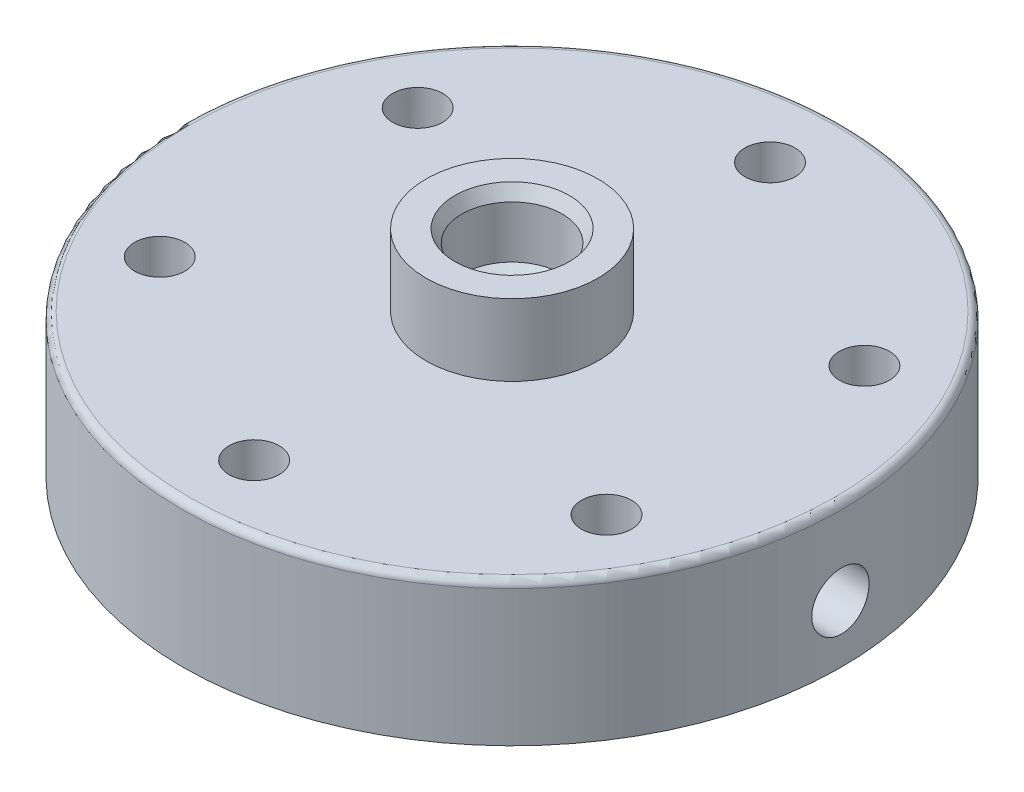
SolidWorks part; units mm, degrees
ref_plane "Front Plane" through (0, 0, 0) normal (0, 0, 1) x (1, 0, 0)
ref_plane "Top Plane" through (0, 0, 0) normal (0, 1, 0) x (1, 0, 0)
ref_plane "Right Plane" through (0, 0, 0) normal (1, 0, 0) x (0, 0, -1)
sketch "Sketch3" plane through (0, 0, 0) normal (0, 1, 0) x (1, 0, 0)
  circle A0 centre (0, 0) radius 46
  circle A1 centre (0, 0) radius 36 construction
  circle A2 centre (0, 36) radius 3.5
  circle A3 centre (31.1769, 18) radius 3.5
  circle A4 centre (31.1769, -18) radius 3.5
  circle A5 centre (0, -36) radius 3.5
  circle A6 centre (-31.1769, -18) radius 3.5
  circle A7 centre (-31.1769, 18) radius 3.5
  dimension "D1" = 92
  dimension "D2" = 72
  dimension "D3" = 7
  dimension "D4" = 6
extrude "Boss-Extrude2" add sketch "Sketch3" along normal blind 20
fillet "Fillet1" radius 1 1 edges at (0, 20, 46)
sketch "Sketch4" plane through (0, 20, 0) normal (0, 1, 0) x (1, 0, 0)
  circle A0 centre (0, 0) radius 12
  dimension "D1" = 24
extrude "Boss-Extrude3" add sketch "Sketch4" along normal blind 10
sketch "Sketch5" plane through (0, 0, 0) normal (0, -1, 0) x (1, 0, 0)
  circle A0 centre (0, 0) radius 33
  dimension "D1" = 66
extrude "Cut-Extrude1" cut sketch "Sketch5" against normal blind 14
sketch "Sketch6" plane through (0, 14, 0) normal (0, -1, 0) x (1, 0, 0)
  circle A0 centre (0, 0) radius 2.5
  dimension "D1" = 5
extrude "Cut-Extrude2" cut sketch "Sketch6" against normal blind 6
sketch "Sketch7" plane through (0, 30, 0) normal (0, 1, 0) x (1, 0, 0)
  circle A0 centre (0, 0) radius 7
  dimension "D1" = 14
extrude "Cut-Extrude3" cut sketch "Sketch7" against normal blind 10
cosmetic thread "Cosmetic Thread1" parameters "D1"=9, "D2"=16
cosmetic thread "Cosmetic Thread2" parameters "D1"=9, "D2"=16
chamfer "Chamfer1" distance 1 angle 60 2 edges at (0, 30, 7) (0, 20, 7)
sketch "Sketch8" plane through (0, 0, 0) normal (1, 0, 0) x (0, 0, -1)
  line L0 (-46, 0) -> (46, 0) construction
  circle A0 centre (0, 8) radius 4
  dimension "D1" = 8
  dimension "D2" = 8
extrude "Cut-Extrude4" cut sketch "Sketch8" along normal through all
